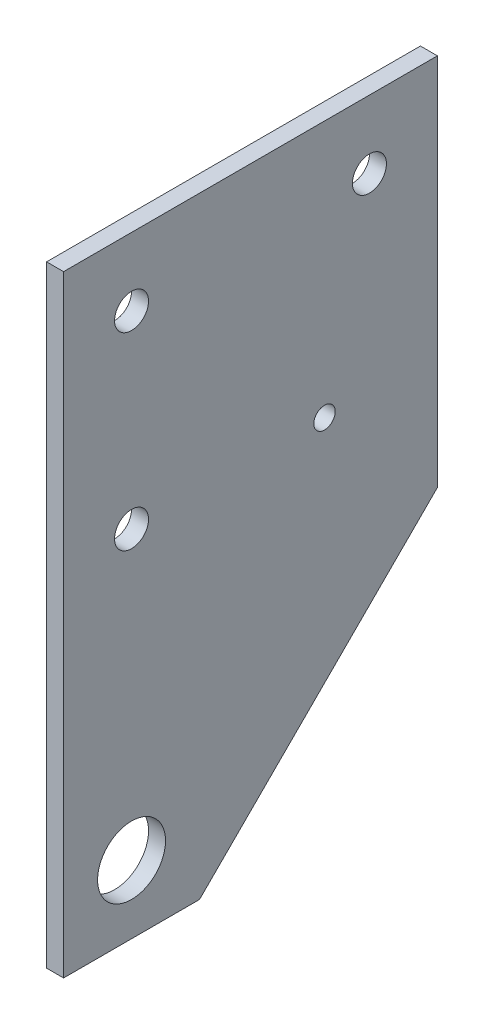
SolidWorks part; units mm, degrees
ref_plane "Front Plane" through (0, 0, 0) normal (0, 0, 1) x (1, 0, 0)
ref_plane "Top Plane" through (0, 0, 0) normal (0, 1, 0) x (1, 0, 0)
ref_plane "Right Plane" through (0, 0, 0) normal (1, 0, 0) x (0, 0, -1)
sketch "Sketch1" plane through (0, 0, 0) normal (1, 0, 0) x (0, 0, -1)
  line L0 (-12.7, 101.6) -> (57.15, 101.6)
  line L1 (12.7, -12.7) -> (57.15, 31.75)
  line L2 (57.15, 31.75) -> (57.15, 101.6)
  line L4 (-12.7, -12.7) -> (12.7, -12.7)
  line L6 (-12.7, 101.6) -> (-12.7, -12.7)
  circle A0 centre (36.0553, 53.601) radius 2
  circle A2 centre (0, 0) radius 6.35
  circle A3 centre (0, 0) radius 61.595 construction
  circle A4 centre (0, 88.9) radius 3.175
  circle A5 centre (44.45, 88.9) radius 3.175
  circle A6 centre (0, 53.601) radius 3.175
  circle A11 centre (36.0553, 53.601) radius 2 construction
  point P11 (0, -12.7)
  dimension "D4" = 69.85
  dimension "D6" = 12.7
  dimension "D8" = 123.19
  dimension "D9" = 6.35
  dimension "D11" = 12.7
  dimension "D12" = 12.7
  dimension "D7" = 6.35
  dimension "D14" = 6.35
  dimension "D1" = 25.4
  dimension "D2" = 69.85
  dimension "D3" = 114.3
  dimension "D5" = 12.7
  dimension "D10" = 12.7
  dimension "D13" = 12.7
extrude "Boss-Extrude1" add sketch "Sketch1" along normal blind 3.175
